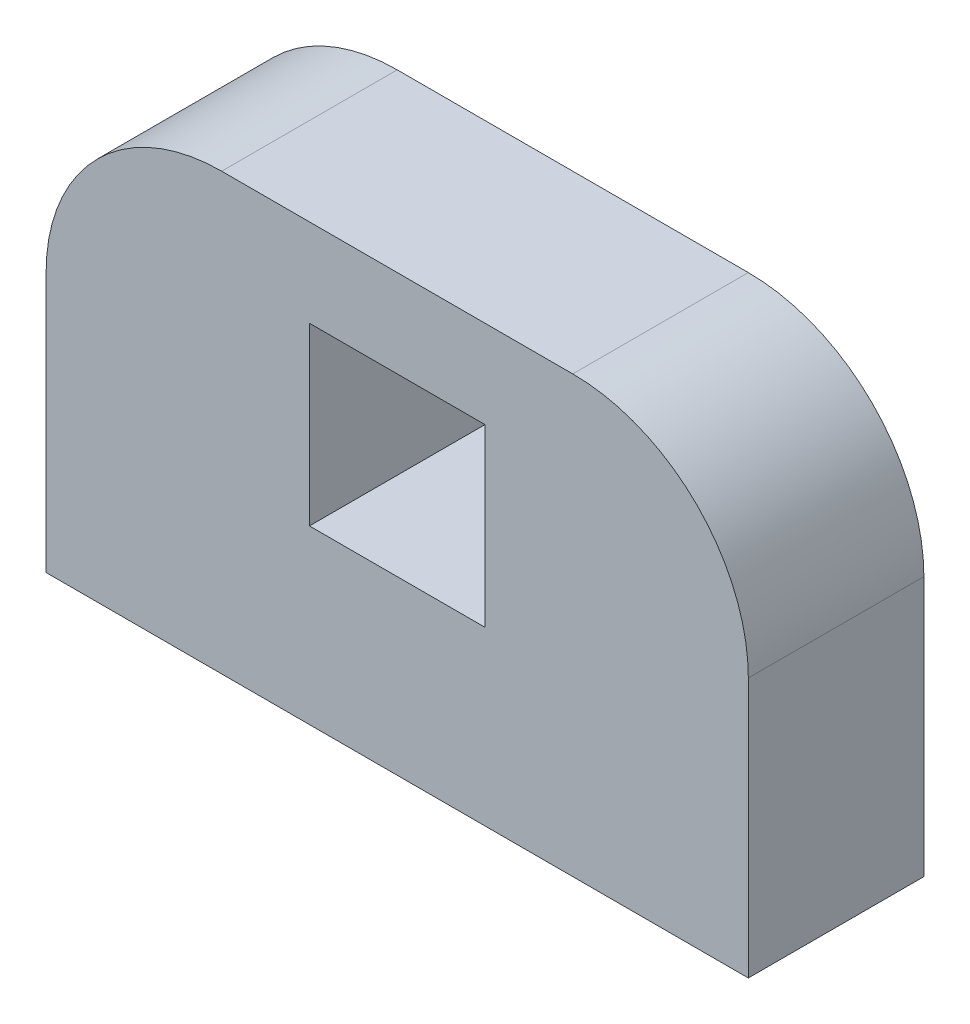
SolidWorks part; units mm, degrees
ref_plane "Front Plane" through (0, 0, 0) normal (0, 0, 1) x (1, 0, 0)
ref_plane "Top Plane" through (0, 0, 0) normal (0, 1, 0) x (1, 0, 0)
ref_plane "Right Plane" through (0, 0, 0) normal (1, 0, 0) x (0, 0, -1)
sketch "Sketch1" plane through (0, 0, 0) normal (0, 0, 1) x (1, 0, 0)
  line L1 (0, 0) -> (12.7, 0)
  line L2 (0, 0) -> (0, 4.699)
  line L3 (3.175, 7.874) -> (9.525, 7.874)
  line L4 (12.7, 0) -> (12.7, 4.699)
  line L5 (4.7625, 6.2865) -> (7.9375, 6.2865)
  line L6 (4.7625, 6.2865) -> (4.7625, 3.1115)
  line L7 (4.7625, 3.1115) -> (7.9375, 3.1115)
  line L8 (7.9375, 6.2865) -> (7.9375, 3.1115)
  arc A0 (9.525, 7.874) -> (12.7, 4.699) centre (9.525, 4.699) cw
  arc A1 (0, 4.699) -> (3.175, 7.874) centre (3.175, 4.699) cw
  point P13 (6.35, 6.2865)
  point P14 (6.35, 7.874)
  dimension "D3" = 3.175
  dimension "D1" = 12.7
  dimension "D2" = 7.874
  dimension "D4" = 3.175
  dimension "D5" = 3.175
  dimension "D6" = 1.5875
extrude "Boss-Extrude1" add sketch "Sketch1" along normal blind 3.175
